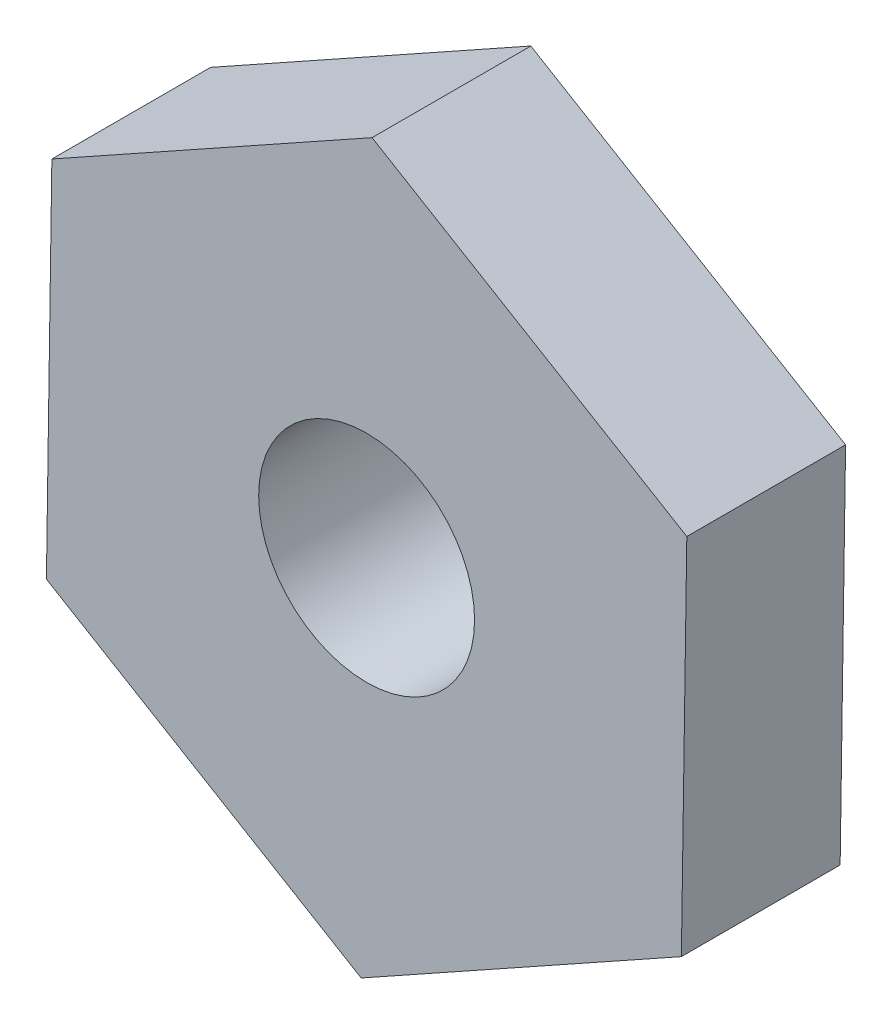
SolidWorks part; units mm, degrees
ref_plane "Front Plane" through (0, 0, 0) normal (0, 0, 1) x (1, 0, 0)
ref_plane "Top Plane" through (0, 0, 0) normal (0, 1, 0) x (1, 0, 0)
ref_plane "Right Plane" through (0, 0, 0) normal (1, 0, 0) x (0, 0, -1)
sketch "Sketch1" plane through (0, 0, 0) normal (0, 0, 1) x (1, 0, 0)
  line L1 (9.9133, -5.9212) -> (10.0845, 5.6245)
  line L2 (10.0845, 5.6245) -> (0.1713, 11.5457)
  line L3 (0.1713, 11.5457) -> (-9.9133, 5.9212)
  line L4 (-9.9133, 5.9212) -> (-10.0845, -5.6245)
  line L5 (-10.0845, -5.6245) -> (-0.1713, -11.5457)
  line L6 (-0.1713, -11.5457) -> (9.9133, -5.9212)
  circle A0 centre (0, 0) radius 10 construction
  dimension "D1" = 20
extrude "Boss-Extrude1" add sketch "Sketch1" along normal blind 5
hole_wizard "M8 Tapped Hole1" positions "Sketch3" profile "Sketch2" tap size "M8" standard "ISO"
sketch "Sketch3" plane through (0, 0, 5) normal (0, 0, 1) x (1, 0, 0)
  point P0 (0, 0)
sketch "Sketch2" plane through (0, 0, 5) normal (1, 0, 0) x (0, -1, 0)
  line L0 (0, 0) -> (0, 21.7929)
  line L1 (0, 21.7929) -> (3.4, 19.75)
  line L2 (3.4, 19.75) -> (3.4, 0)
  line L5 (3.4, 0) -> (0, 0)
  line L10 (0, 21.7929) -> (-3.4, 19.75) construction
  line L11 (0, -6.35) -> (0, 107.95) construction
  dimension "Tap Drill Dia." = 6.8
  dimension "Tap Drill Depth" = 19.75
  dimension "Drill Angle" = 118
cosmetic thread "Hole Thread1" parameters "D1"=5, "D2"=8
